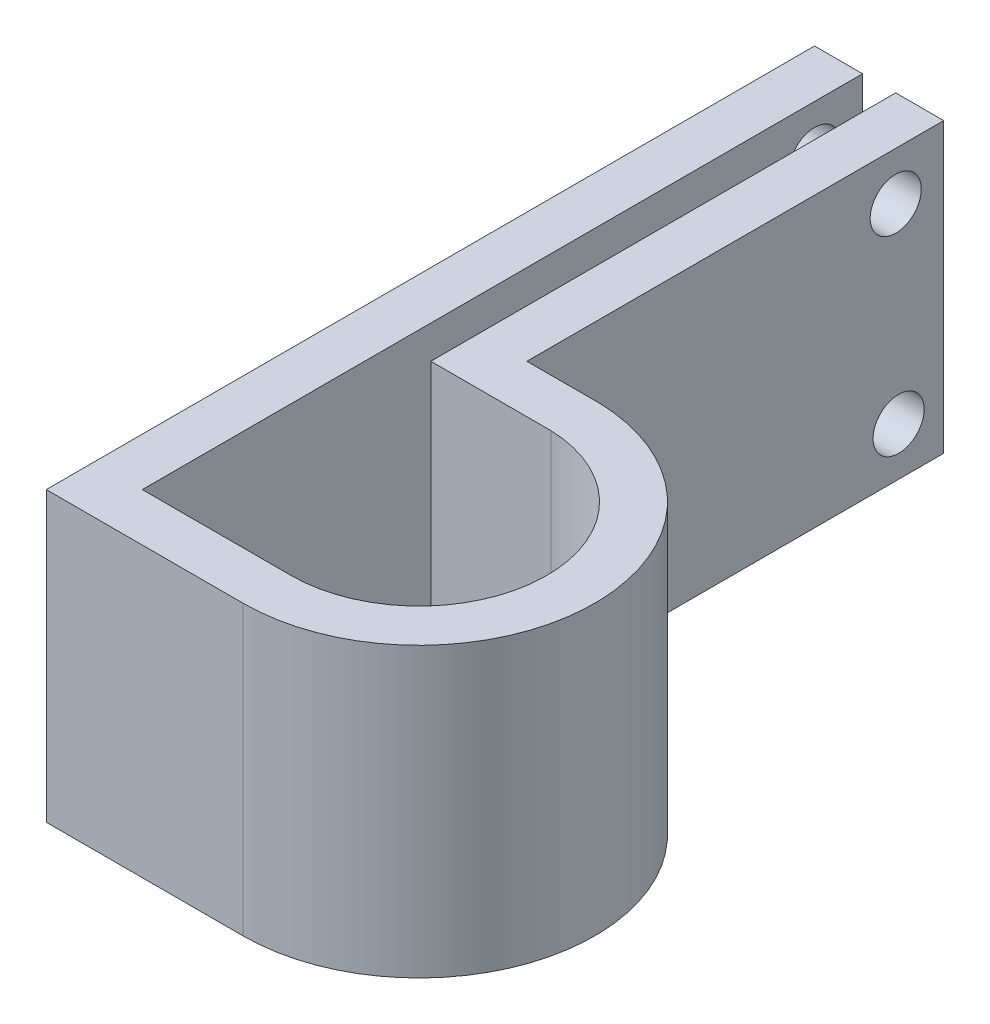
SolidWorks part; units mm, degrees
ref_plane "Front Plane" through (0, 0, 0) normal (0, 0, 1) x (1, 0, 0)
ref_plane "Top Plane" through (0, 0, 0) normal (0, 1, 0) x (1, 0, 0)
ref_plane "Right Plane" through (0, 0, 0) normal (1, 0, 0) x (0, 0, -1)
sketch "Sketch1" plane through (0, 0, 0) normal (0, 1, 0) x (1, 0, 0)
  line L0 (-0.0085, -16.891) -> (-19.6935, -16.891)
  line L1 (-19.6935, -16.891) -> (-19.6935, 78.359)
  line L2 (0.563, 16.8816) -> (-15.312, 16.8816)
  line L3 (-15.312, 16.8816) -> (-15.312, 78.359)
  line L4 (-19.6935, 14.922) -> (-16.582, 14.922) construction
  line L5 (-19.6935, 14.922) -> (-19.6935, -16.2571) construction
  line L6 (-19.6935, -16.2571) -> (-16.582, -16.2571) construction
  line L7 (-16.582, 14.922) -> (-16.582, -16.2571) construction
  line L8 (-15.312, 78.359) -> (-19.6935, 78.359) construction
  line L9 (-15.312, 78.359) -> (-8.962, 78.359)
  line L10 (-8.962, 78.359) -> (-8.962, 23.2316)
  line L11 (-8.962, 23.2316) -> (0.6604, 23.2316)
  line L12 (0, -23.241) -> (-26.0435, -23.241)
  line L13 (-26.0435, -23.241) -> (-26.0435, 78.359)
  line L14 (-26.0435, 78.359) -> (-19.6935, 78.359)
  arc A0 (0.563, 16.8816) -> (-0.0085, -16.891) centre (0, 0) cw
  circle A1 centre (0, 0) radius 15.875 construction
  arc A2 (0.6604, 23.2316) -> (0, -23.241) centre (0, 0) cw
  dimension "D4" = 31.75
  dimension "D14" = 16.891
  dimension "D2" = 19.685
  dimension "D3" = 6.35
  dimension "D5" = 15.875
  dimension "D6" = 3.1115
  dimension "D7" = 61.4774
  dimension "D8" = 6.35
  dimension "D9" = 6.35
  dimension "D10" = 55.1274
  dimension "D11" = 4.3815
  dimension "D12" = 101.6
  dimension "D13" = 6.35
  dimension "D15" = 1.27
extrude "Boss-Extrude1" add sketch "Sketch1" along normal blind 38.1
sketch "Sketch2" plane through (-8.962, 0, 0) normal (1, 0, 0) x (0, 0, -1)
  line L0 (-23.241, 38.1) -> (-23.241, 0) construction
  line L1 (23.2316, 38.1) -> (78.359, 38.1) construction
  line L2 (78.359, 38.1) -> (78.359, 0) construction
  line L3 (23.2316, 0) -> (78.359, 0) construction
  circle A0 centre (72.009, 31.75) radius 3.3782
  circle A1 centre (72.39, 6.3529) radius 3.3782
  point P10 (66.04, 9.525)
  point P11 (0, 0)
  point P14 (72.39, 9.525)
  dimension "D1" = 6.7564
  dimension "D2" = 6.35
  dimension "D3" = 6.35
  dimension "D4" = 25.4
  dimension "D5" = 6.3529
  dimension "D6" = 95.631
extrude "Cut-Extrude1" cut sketch "Sketch2" against normal through all
